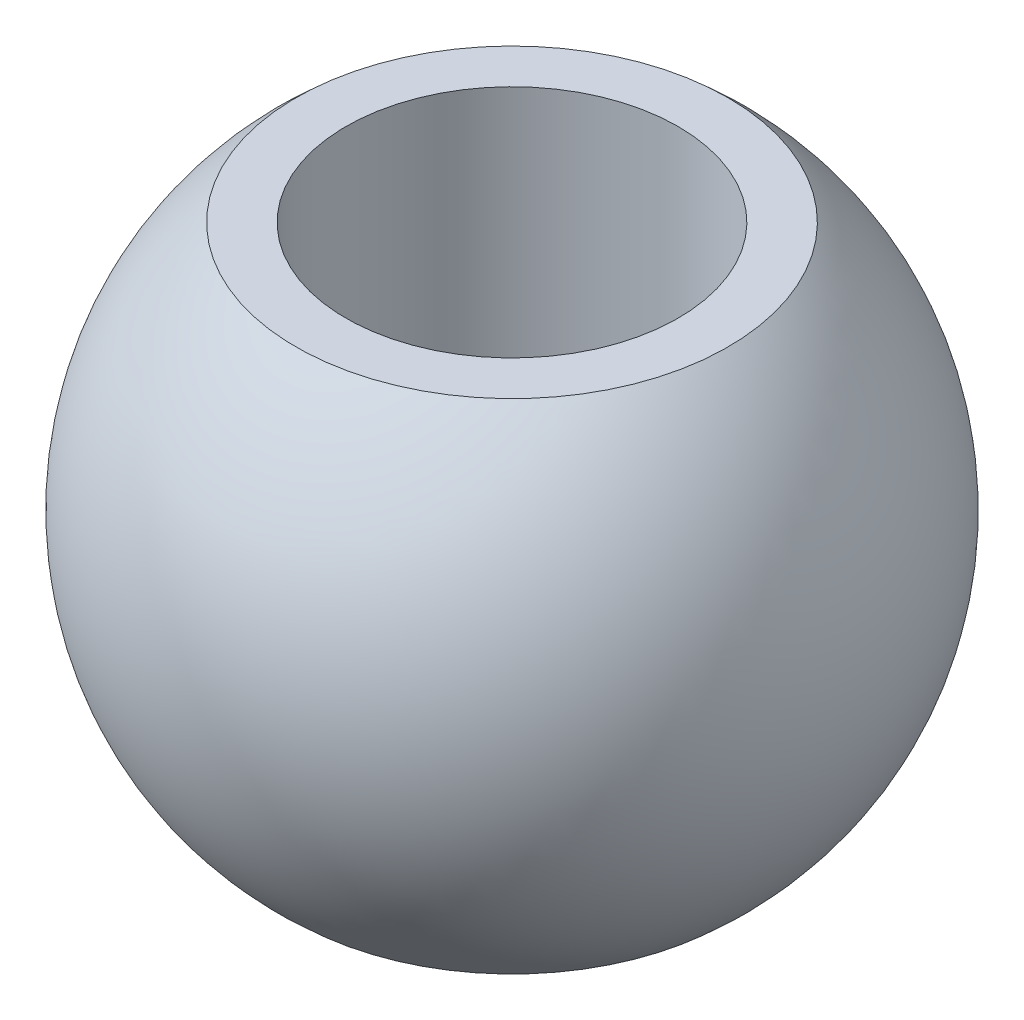
SolidWorks part; units mm, degrees
material "1.0545 (S355N)"
ref_plane "Płaszczyzna przednia" through (0, 0, 0) normal (0, 0, 1) x (1, 0, 0)
ref_plane "Płaszczyzna górna" through (0, 0, 0) normal (0, 1, 0) x (1, 0, 0)
ref_plane "Płaszczyzna prawa" through (0, 0, 0) normal (1, 0, 0) x (0, 0, -1)
sketch "Szkic1" plane through (0, 0, 0) normal (0, 0, 1) x (1, 0, 0)
  line L0 (0, -11.1) -> (0, 11.1) construction
  line L1 (4, -6) -> (4, 6)
  line L2 (4, 6) -> (5.2003, 6)
  line L3 (4, -6) -> (5.2003, -6)
  arc A0 (5.2003, -6) -> (5.2003, 6) centre (0, 0) ccw
  point P6 (4, 0)
  dimension "d3" = 15.88
  dimension "d1" = 4
  dimension "b1" = 12
revolve "Obrót1" add sketch "Szkic1" angle 360 about L0
